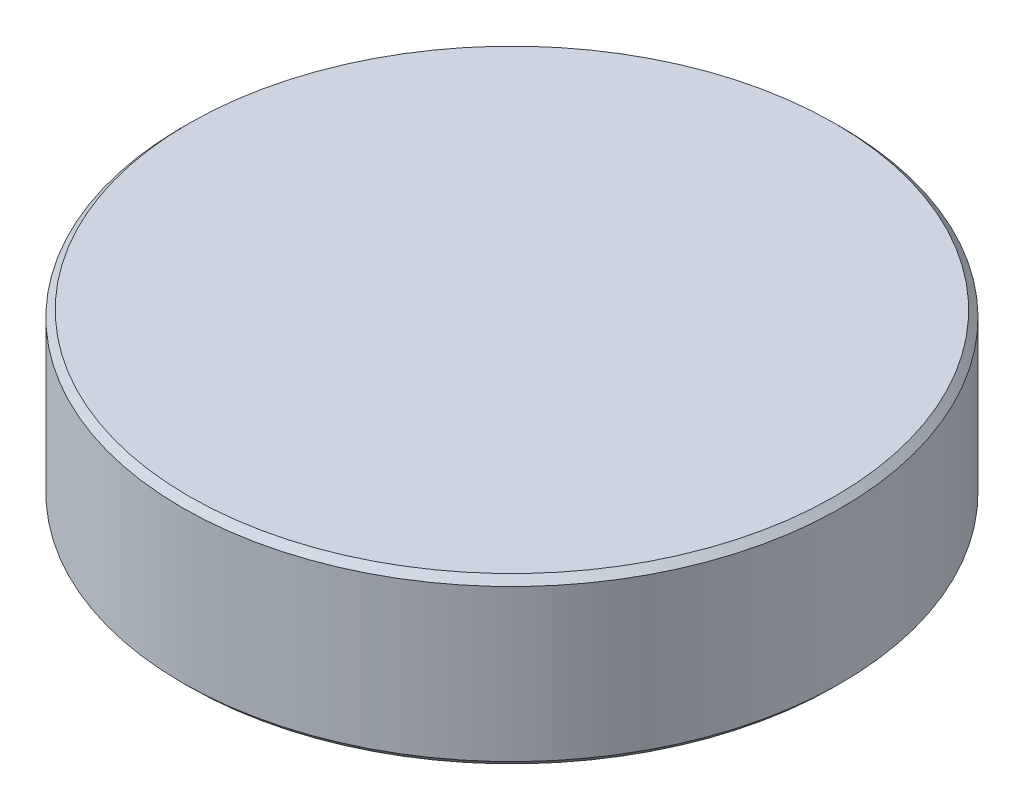
SolidWorks part; units mm, degrees
ref_plane "Plan de face" through (0, 0, 0) normal (0, 0, 1) x (1, 0, 0)
ref_plane "Plan de dessus" through (0, 0, 0) normal (0, 1, 0) x (1, 0, 0)
ref_plane "Plan de droite" through (0, 0, 0) normal (1, 0, 0) x (0, 0, -1)
sketch "Esquisse1" plane through (0, 0, 0) normal (0, 0, 1) x (1, 0, 0)
  line L0 (-98, 25) -> (-100, 23)
  line L1 (0, 25) -> (-98, 25)
  line L2 (-100, 23) -> (-100, -23)
  line L3 (-98, -25) -> (0, -25)
  line L4 (-100, -23) -> (-98, -25)
  line L5 (0, 25) -> (0, -31.8779) construction
  line L6 (0, 25) -> (0, -25)
  point P3 (-100, 25)
  point P5 (-100, -25)
revolve "Révolution1" add sketch "Esquisse1" angle 360 about L5
